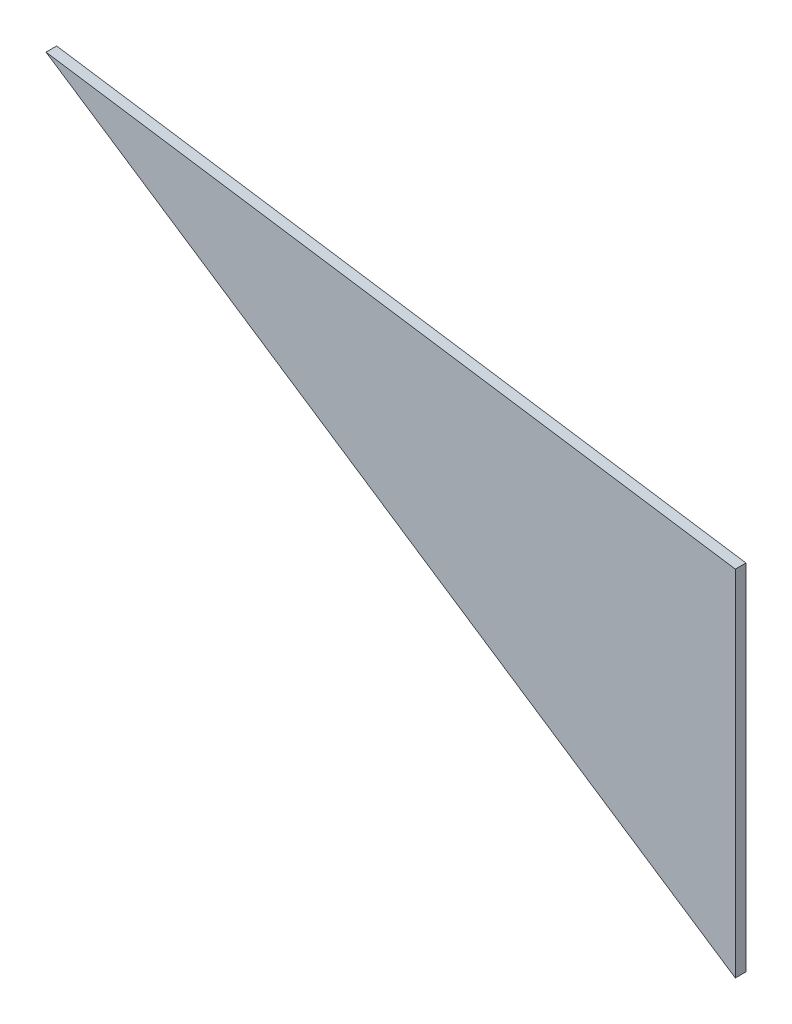
SolidWorks part; units mm, degrees
material "Stop 1060"
ref_plane "Front Plane" through (0, 0, 0) normal (0, 0, 1) x (1, 0, 0)
ref_plane "Top Plane" through (0, 0, 0) normal (0, 1, 0) x (1, 0, 0)
ref_plane "Right Plane" through (0, 0, 0) normal (1, 0, 0) x (0, 0, -1)
sketch "Szkic1" plane through (0, 0, 0) normal (0, 0, 1) x (1, 0, 0)
  line L6 (-210.6801, 173.3732) -> (-210.6801, -159.8256)
  line L7 (-210.6801, -159.8256) -> (-859.317, 270.3406)
  line L8 (-210.6801, 173.3732) -> (-859.317, 270.3406)
extrude "Dodanie-wyciągnięcie1" add sketch "Szkic1" along normal blind 10
